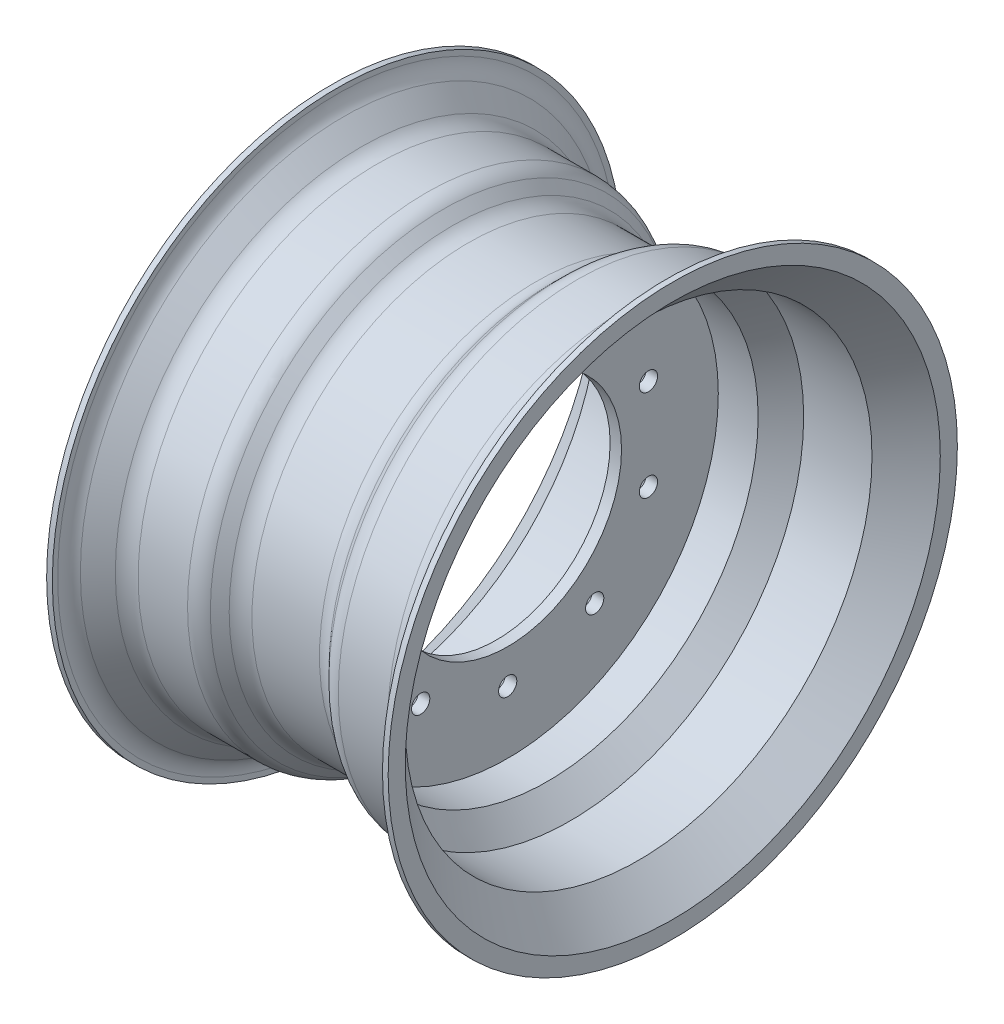
SolidWorks part; units mm, degrees
ref_plane "Front Plane" through (0, 0, 0) normal (0, 0, 1) x (1, 0, 0)
ref_plane "Top Plane" through (0, 0, 0) normal (0, 1, 0) x (1, 0, 0)
ref_plane "Right Plane" through (0, 0, 0) normal (1, 0, 0) x (0, 0, -1)
sketch "Sketch4" plane through (0, 0, 0) normal (0, 0, 1) x (1, 0, 0)
  line L0 (0, 0) -> (0, 266.656) construction
  line L1 (0, 0) -> (-375.6186, 0) construction
  line L2 (-150, 250) -> (-150, 235)
  line L3 (-150, 235) -> (-120, 205)
  line L4 (-120, 205) -> (-60, 205)
  line L5 (-60, 205) -> (-40, 185)
  line L6 (-40, 185) -> (-5, 185)
  line L7 (60, 205) -> (40, 185)
  line L8 (120, 205) -> (60, 205)
  line L9 (150, 235) -> (120, 205)
  line L10 (150, 250) -> (150, 235)
  line L11 (-145, 250) -> (-145, 237.0711)
  line L12 (-145, 237.0711) -> (-117.9289, 210)
  line L13 (-117.9289, 210) -> (-57.9289, 210)
  line L14 (-57.9289, 210) -> (-37.9289, 190)
  line L15 (-37.9289, 190) -> (37.9289, 190)
  line L16 (57.9289, 210) -> (37.9289, 190)
  line L17 (117.9289, 210) -> (57.9289, 210)
  line L18 (145, 237.0711) -> (117.9289, 210)
  line L19 (145, 250) -> (145, 237.0711)
  line L20 (-150, 250) -> (-145, 250)
  line L21 (145, 250) -> (150, 250)
  line L22 (5, 185) -> (40, 185)
  line L24 (-5, 185) -> (-5, 100)
  line L25 (-5, 100) -> (5, 100)
  line L26 (5, 185) -> (5, 100)
  line L27 (-40, 185) -> (40, 185) construction
  point P11 (0, 185)
  dimension "D1" = 250
  dimension "D2" = 15
  dimension "D3" = 30
  dimension "D4" = 60
  dimension "D5" = 20
  dimension "D6" = 40
  dimension "D7" = 135
  dimension "D8" = 135
  dimension "D10" = 10
  dimension "D11" = 5
  dimension "D12" = 100
  dimension "D13" = 150
  dimension "D9" = 5
revolve "Revolve1" add sketch "Sketch4" angle 360 about L1
fillet "Fillet1" radius 20 8 edges at (145, 0, -237.0711) (117.9289, 0, -210) (57.9289, 0, -210) (37.9289, 0, -190) (-37.9289, 0, -190) (-57.9289, 0, -210) (-117.9289, 0, -210) (-145, 0, -237.0711)
sketch "Sketch5" plane through (5, 0, 0) normal (1, 0, 0) x (0, 0, -1)
  circle A0 centre (0, 130) radius 8
  point P2 (0, 0)
  dimension "D1" = 16
  dimension "D2" = 130
extrude "Cut-Extrude1" cut sketch "Sketch5" against normal through all
pattern_circular "CirPattern1" count 10 over 360 about axis through (0, 0, 0) along (1, 0, 0) of "Cut-Extrude1"
